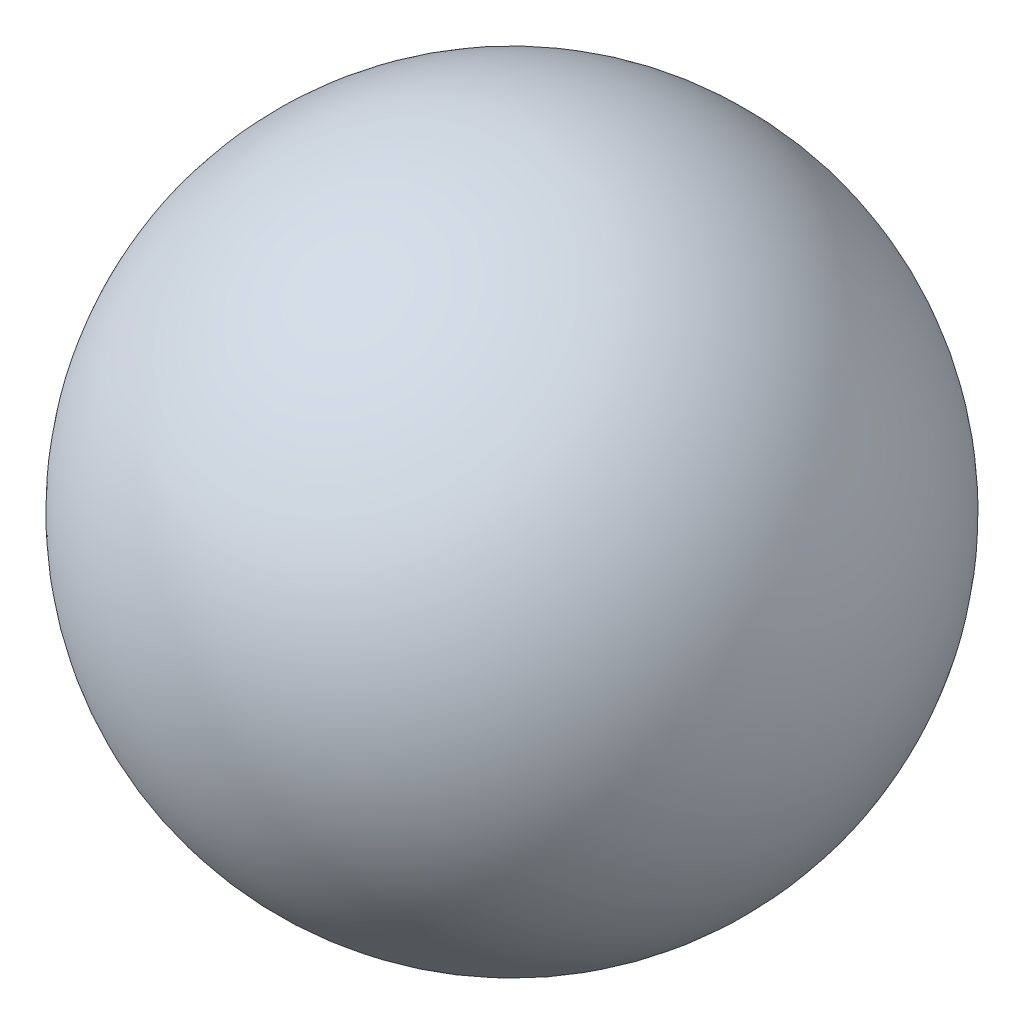
SolidWorks part; units mm, degrees
material "Rubber"
ref_plane "Front Plane" through (0, 0, 0) normal (0, 0, 1) x (1, 0, 0)
ref_plane "Top Plane" through (0, 0, 0) normal (0, 1, 0) x (1, 0, 0)
ref_plane "Right Plane" through (0, 0, 0) normal (1, 0, 0) x (0, 0, -1)
sketch "Sketch1" plane through (0, 0, 0) normal (0, 0, 1) x (1, 0, 0)
  line L2 (-34, 0) -> (-32.5, 0)
  line L3 (-32.5, 0) -> (32.5, 0) construction
  line L4 (32.5, 0) -> (34, 0)
  arc A2 (34, 0) -> (-34, 0) centre (0, 0) ccw
  arc A3 (32.5, 0) -> (-32.5, 0) centre (0, 0) ccw
  arc A4 (-34, 0) -> (34, 0) centre (0, 0) ccw construction
  arc A5 (-32.5, 0) -> (32.5, 0) centre (0, 0) ccw construction
  dimension "D1" = 68
  dimension "D2" = 1.5
revolve "Revolve1" add sketch "Sketch1" angle 360 about L3
